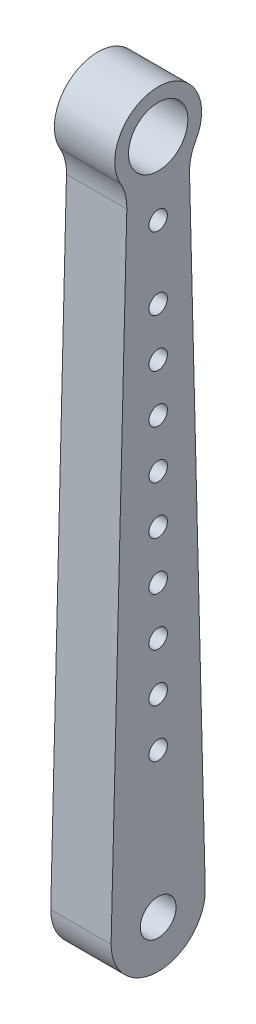
SolidWorks part; units mm, degrees
material "6061-T6 (SS)"
ref_plane "Front Plane" through (0, 0, 0) normal (0, 0, 1) x (1, 0, 0)
ref_plane "Top Plane" through (0, 0, 0) normal (0, 1, 0) x (1, 0, 0)
ref_plane "Right Plane" through (0, 0, 0) normal (1, 0, 0) x (0, 0, -1)
sketch "Outline Front" plane through (0, 0, 0) normal (0, 0, 1) x (1, 0, 0)
  line L0 (0, 254) -> (0, -25.4) construction
  line L1 (0, 0) -> (-76.2, 0) construction
  line L2 (-76.2, 0) -> (-76.2, 254) construction
  line L3 (-76.2, 254) -> (0, 254) construction
  line L4 (-76.2, -25.4) -> (0, -25.4) construction
  line L5 (-76.2, 177.8) -> (0, 177.8) construction
  line L6 (-76.2, 203.2) -> (0, 203.2) construction
  point P3 (0, 0)
  dimension "D1" = 279.4
  dimension "D2" = 25.4
  dimension "D3" = 76.2
  dimension "D4" = 177.8
  dimension "D5" = 203.2
sketch "Outline Side" plane through (0, 0, 0) normal (1, 0, 0) x (0, 0, -1)
  line L0 (0, 254) -> (0, -25.4) construction
  line L1 (0, 0) -> (0, 254) construction
  circle A0 centre (0, 0) radius 4.7117 construction
  circle A1 centre (0, 177.8) radius 7.9375 construction
  circle A2 centre (0, 63.5) radius 2.413 construction
  circle A3 centre (0, 50.8) radius 2.413 construction
  circle A4 centre (0, 76.2) radius 2.413 construction
  circle A5 centre (0, 88.9) radius 2.413 construction
  circle A6 centre (0, 101.6) radius 2.413 construction
  circle A7 centre (0, 114.3) radius 2.413 construction
  circle A8 centre (0, 127) radius 2.413 construction
  circle A9 centre (0, 139.7) radius 2.413 construction
  circle A10 centre (0, 158.75) radius 2.413 construction
  circle A12 centre (0, 38.1) radius 2.413 construction
  dimension "D1" = 9.4234
  dimension "D2" = 15.875
  dimension "D3" = 4.826
  dimension "D4" = 63.5
  dimension "D5" = 177.8
  dimension "D6" = 50.8
  dimension "D7" = 76.2
  dimension "D8" = 88.9
  dimension "D9" = 101.6
  dimension "D10" = 114.3
  dimension "D11" = 127
  dimension "D12" = 139.7
  dimension "D13" = 158.75
  dimension "D15" = 38.1
sketch "Sketch3" plane through (0, 0, 0) normal (1, 0, 0) x (0, 0, -1)
  line L0 (0, 177.7405) -> (0, -12.7) construction
  line L1 (-12.7, -12.7) -> (12.7, -12.7)
  line L2 (-12.7, -12.7) -> (-7.9375, 177.7405) construction
  line L3 (-7.9375, 177.7405) -> (7.9375, 177.7405) construction
  line L4 (12.7, -12.7) -> (7.9375, 177.7405) construction
  line L5 (-8.1382, 169.7146) -> (-12.7, -12.7)
  line L6 (8.1382, 169.7146) -> (12.7, -12.7)
  arc A0 (8.1382, 169.7146) -> (-8.1382, 169.7146) centre (0, 177.7405) ccw
  dimension "D5" = 22.86
  dimension "D1" = 190.5
  dimension "D2" = 25.4
  dimension "D3" = 12.7
  dimension "D4" = 15.875
extrude "Vertical Bar" add sketch "Sketch3" against normal blind 15.875
sketch "Sketch5" plane through (0, 0, 0) normal (1, 0, 0) x (0, 0, -1)
  circle A0 centre (0, 50.8) radius 2.413
  circle A1 centre (0, 63.5) radius 2.413
  circle A2 centre (0, 76.2) radius 2.413
  circle A3 centre (0, 63.5) radius 2.413 construction
  circle A4 centre (0, 88.9) radius 2.413
  circle A5 centre (0, 101.6) radius 2.413
  circle A6 centre (0, 88.9) radius 2.413 construction
  circle A7 centre (0, 101.6) radius 2.413 construction
  circle A8 centre (0, 114.3) radius 2.413
  circle A9 centre (0, 127) radius 2.413
  circle A10 centre (0, 139.7) radius 2.413
  circle A11 centre (0, 158.75) radius 2.413
  circle A13 centre (0, 114.3) radius 2.413 construction
  circle A14 centre (0, 38.1) radius 2.413
  circle A15 centre (0, 38.1) radius 2.413 construction
extrude "Cut-Cable holder" cut sketch "Sketch5" against normal up to next
sketch "Sketch6" plane through (0, 0, 0) normal (1, 0, 0) x (0, 0, -1)
  circle A0 centre (0, 0) radius 4.7117
  circle A1 centre (0, 0) radius 4.7117 construction
extrude "Cut-Pivot hole" cut sketch "Sketch6" against normal up to next
sketch "Sketch8" plane through (0, 0, 0) normal (1, 0, 0) x (0, 0, -1)
  line L0 (-12.3824, 0) -> (-12.7, -12.7)
  line L1 (12.7, -12.7) -> (8.1382, 169.7146) construction
  line L3 (-12.7, -12.7) -> (12.7, -12.7)
  line L4 (12.7, -12.7) -> (12.3824, 0)
  line L5 (-12.7, -12.7) -> (12.7, -12.7) construction
  arc A0 (-12.3824, 0) -> (12.3824, 0) centre (0, 0) ccw
  point P2 (0, -12.7)
  dimension "D1" = 25.4
extrude "Cut-Extrude8" cut sketch "Sketch8" against normal through all
sketch "Sketch9" plane through (-15.875, 0, 0) normal (-1, 0, 0) x (0, 0, 1)
  line L0 (0, 140.97) -> (0, 31.75) construction
  line L1 (0, 254) -> (0, -25.4) construction
  line L2 (-6.35, 140.97) -> (-6.35, 31.75)
  line L4 (6.35, 140.97) -> (6.35, 31.75)
  arc A0 (-6.35, 31.75) -> (6.35, 31.75) centre (0, 31.75) ccw
  arc A1 (-6.35, 140.97) -> (6.35, 140.97) centre (0, 140.97) cw
  dimension "D3" = 31.75
  dimension "D2" = 6.35
  dimension "D1" = 109.22
extrude "Slot Cut" cut sketch "Sketch9" against normal blind 7.62
sketch "Sketch10" plane through (0, 0, 0) normal (1, 0, 0) x (0, 0, -1)
  circle A0 centre (0, 177.8) radius 7.8105
  dimension "D1" = 15.621
extrude "Cut-Extrude9" cut sketch "Sketch10" against normal through all
fillet "Fillet1" radius 12.7 2 edges at (-7.9375, 169.7146, -8.1382) (-7.9375, 169.7146, 8.1382)
